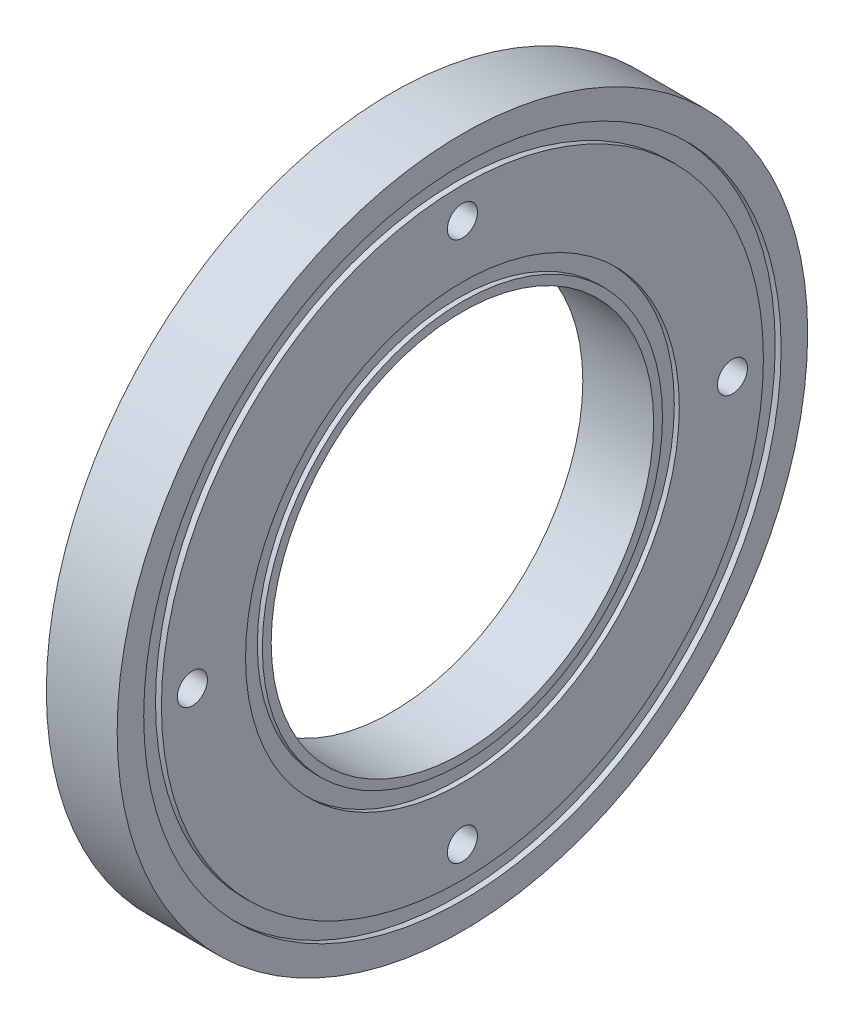
SolidWorks part; units mm, degrees
ref_plane "Front Plane" through (0, 0, 0) normal (0, 0, 1) x (1, 0, 0)
ref_plane "Top Plane" through (0, 0, 0) normal (0, 1, 0) x (1, 0, 0)
ref_plane "Right Plane" through (0, 0, 0) normal (1, 0, 0) x (0, 0, -1)
sketch "Sketch1" plane through (0, 0, 0) normal (0, 0, 1) x (1, 0, 0)
  line L0 (-801.9206, 0) -> (36107.5283, 0) construction
  line L10 (21.0477, 24.5) -> (21.0477, 39)
  line L12 (21.0477, 39) -> (13.0477, 39)
  line L16 (21.0477, 24.5) -> (20.4817, 24.5)
  line L17 (20.4817, 24.5) -> (20.4817, 21.6)
  line L18 (13.0477, 39) -> (13.0477, 24.5)
  line L22 (18.4817, 21.6) -> (20.4817, 21.6)
  line L28 (13.0477, 24.5) -> (13.6137, 24.5)
  line L29 (13.6137, 24.5) -> (13.6137, 21.6)
  line L30 (13.6137, 21.6) -> (18.4817, 21.6)
  line L31 (21.0477, 36) -> (20.3807, 36)
  line L32 (20.3807, 36) -> (20.3807, 34)
  line L33 (20.3807, 34) -> (21.0477, 34)
  line L34 (13.0477, 36) -> (13.7147, 36)
  line L35 (13.7147, 36) -> (13.7147, 34)
  line L36 (13.7147, 34) -> (13.0477, 34)
  line L37 (20.4817, 22.6) -> (21.0477, 22.6)
  line L38 (21.0477, 22.6) -> (21.0477, 21.6)
  line L39 (21.0477, 21.6) -> (20.4817, 21.6)
  line L40 (13.6137, 22.6) -> (13.0477, 22.6)
  line L41 (13.0477, 22.6) -> (13.0477, 21.6)
  line L42 (13.0477, 21.6) -> (13.6137, 21.6)
  dimension "D1" = 8
  dimension "D5" = 39
  dimension "D2" = 36
  dimension "D3" = 0.566
  dimension "D4" = 2
  dimension "D6" = 0.667
  dimension "D7" = 1
  dimension "D8" = 24.5
  dimension "D9" = 2
  dimension "D10" = 1.9
revolve "Revolve17" add sketch "Sketch1" angle 360 about L0
sketch "Sketch4" plane through (13.0477, 0, 0) normal (-1, 0, 0) x (0, 0, 1)
  circle A0 centre (0, 0) radius 30.5 construction
  point P3 (0, 30.5)
  point P7 (30.5, 0)
  point P12 (-30.5, 0)
  point P13 (0, -30.5)
  dimension "D1" = 61
hole_wizard "M3 Clearance Hole1" positions "Sketch4" profile "Sketch5" hole size "M3" standard "ISO"
sketch "Sketch5" plane through (13.0477, -30.5, 0) normal (0, 1, 0) x (0, 0, 1)
  line L0 (0, 0) -> (0, 9.0215)
  line L1 (0, 9.0215) -> (1.7, 8)
  line L2 (1.7, 8) -> (1.7, 0)
  line L5 (1.7, 0) -> (0, 0)
  line L10 (0, 9.0215) -> (-1.7, 8) construction
  line L11 (0, -6.35) -> (0, 107.95) construction
  dimension "Hole Dia." = 3.4
  dimension "Hole Depth" = 8
  dimension "Drill Angle" = 118
